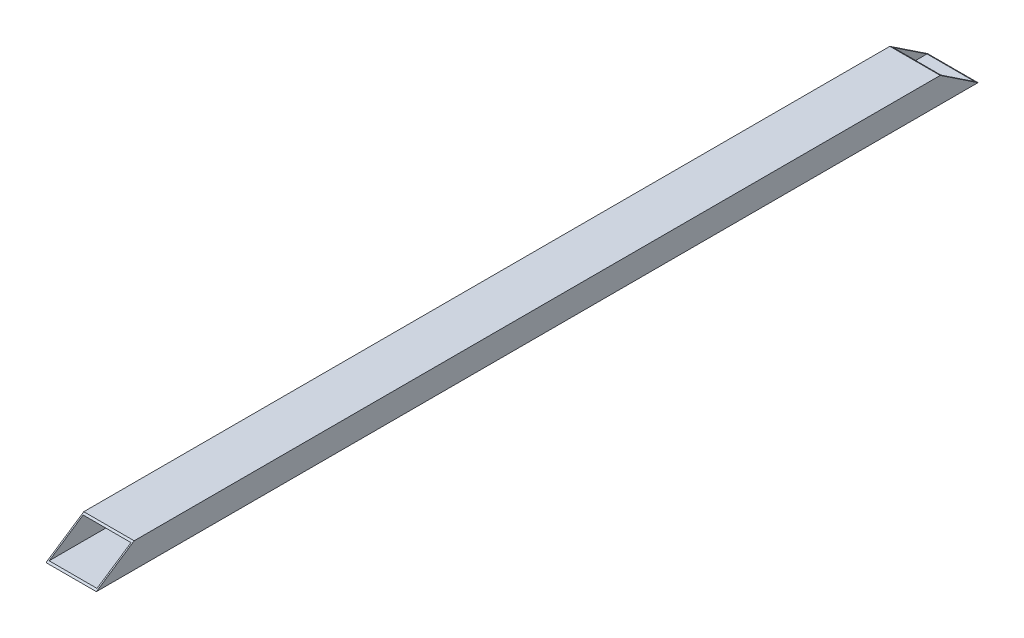
SolidWorks part; units mm, degrees
ref_plane "Front Plane" through (0, 0, 0) normal (0, 0, 1) x (1, 0, 0)
ref_plane "Top Plane" through (0, 0, 0) normal (0, 1, 0) x (1, 0, 0)
ref_plane "Right Plane" through (0, 0, 0) normal (1, 0, 0) x (0, 0, -1)
sketch "Sketch1" plane through (0, 0, 0) normal (0, 0, 1) x (1, 0, 0)
  line L0 (0, 16.2406) -> (0, -17.5231) construction
  line L1 (-25.7305, 0) -> (34.2695, 0) construction
  line L5 (20, -8) -> (0, -8)
  line L6 (0, -8) -> (-20, -8)
  line L11 (-20, -8) -> (-20, 12)
  line L12 (20, -8) -> (20, 12)
  line L13 (-20, 12) -> (20, 12)
  dimension "D1" = 40
  dimension "D2" = 20
  dimension "D5" = 20
  dimension "D6" = 20
  dimension "D9" = 60
extrude "Boss-Extrude1" add sketch "Sketch1" along normal blind 700
sketch "Sketch4" plane through (0, 0, 700) normal (0, 0, 1) x (1, 0, 0)
  line L14 (-19, 11) -> (-19, -7)
  line L15 (-19, -7) -> (19, -7)
  line L16 (19, -7) -> (19, 11)
  line L17 (19, 11) -> (-19, 11)
  line L18 (-19, 11) -> (-19, -7)
  line L19 (-19, -7) -> (19, -7)
  line L20 (19, -7) -> (19, 11)
  line L21 (19, 11) -> (-19, 11)
  dimension "D1" = 1
extrude "Cut-Extrude2" cut sketch "Sketch4" against normal through all
sketch "Sketch3" plane through (-20, 0, 0) normal (-1, 0, 0) x (0, 0, 1)
  line L0 (0, 12) -> (30, 12)
  line L1 (700, 12) -> (0, 12) construction
  line L2 (30, 12) -> (0, -8)
  line L3 (0, -8) -> (0, 12)
  line L4 (670, 12) -> (700, 12)
  line L5 (700, 12) -> (700, -8)
  line L6 (700, -8) -> (670, 12)
  dimension "D1" = 20
  dimension "D2" = 30
  dimension "D3" = 30
  dimension "D4" = 20
extrude "Cut-Extrude1" cut sketch "Sketch3" against normal through all
